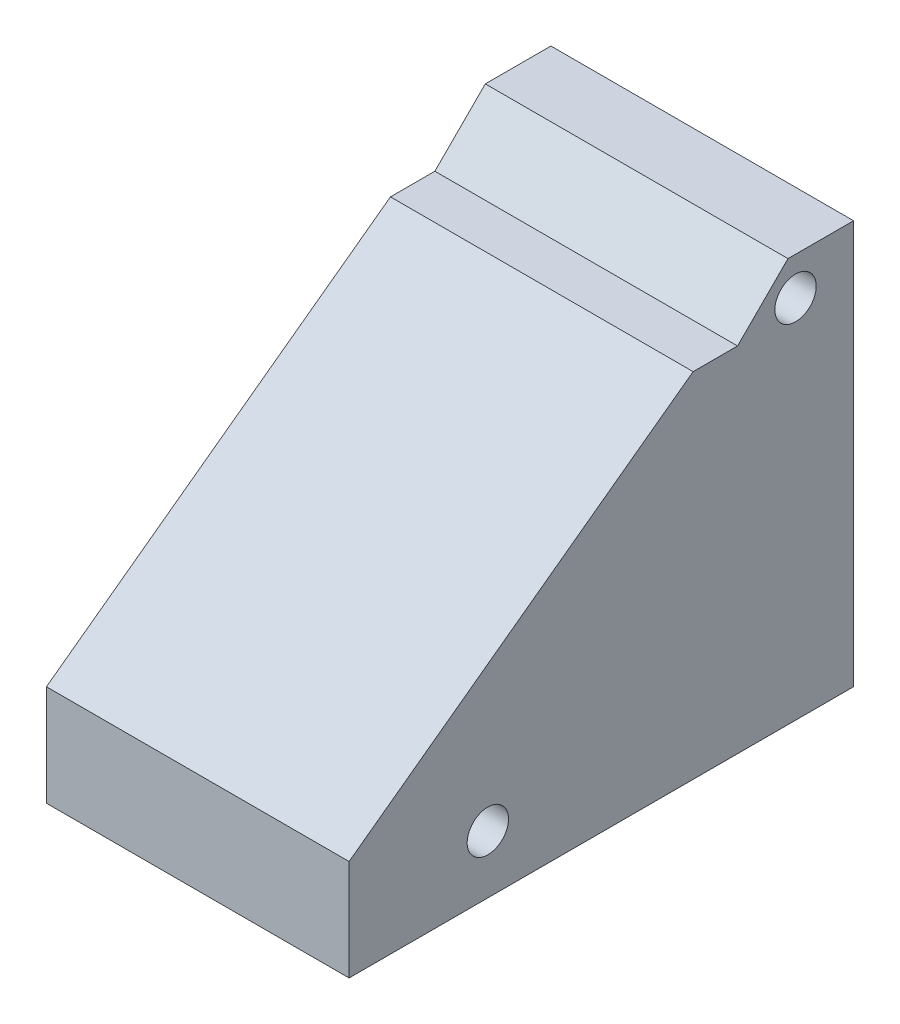
SolidWorks part; units mm, degrees
ref_plane "Спереди" through (0, 0, 0) normal (0, 0, 1) x (1, 0, 0)
ref_plane "Сверху" through (0, 0, 0) normal (0, 1, 0) x (1, 0, 0)
ref_plane "Справа" through (0, 0, 0) normal (1, 0, 0) x (0, 0, -1)
sketch "Sketch1" plane through (0, 0, 0) normal (1, 0, 0) x (0, 0, -1)
  line L0 (0, 0) -> (-100, 0)
  line L1 (-100, 0) -> (-100, 20)
  line L2 (-100, 20) -> (-31.8053, 70.0015)
  line L3 (-31.8053, 70.0015) -> (-22.9985, 70.0015)
  line L4 (-22.9985, 70.0015) -> (-13, 80)
  line L5 (-13, 80) -> (0, 80)
  line L6 (0, 80) -> (0, 0)
  line L7 (-13, 80) -> (-25.5682, 80) construction
  line L8 (-11.5, 72.5) -> (0, 72.5) construction
  line L9 (0, 72.5) -> (0, 0) construction
  line L10 (-72.5, 11.5) -> (-72.5, 0) construction
  line L11 (-72.5, 0) -> (-100, 0) construction
  line L12 (-72.5, 11.5) -> (-100, 0) construction
  circle A0 centre (-11.5, 72.5) radius 4.1
  circle A1 centre (-72.5, 11.5) radius 4.1
  dimension "D8" = 8.2
  dimension "D1" = 100
  dimension "D2" = 20
  dimension "D3" = 8.8068
  dimension "D4" = 80
  dimension "D5" = 13
  dimension "D6" = 45
  dimension "D7" = 14.14
  dimension "D9" = 72.5
  dimension "D10" = 11.5
  dimension "D11" = 27.5
  dimension "D12" = 11.5
extrude "Boss-Extrude1" add sketch "Sketch1" along normal blind 60
